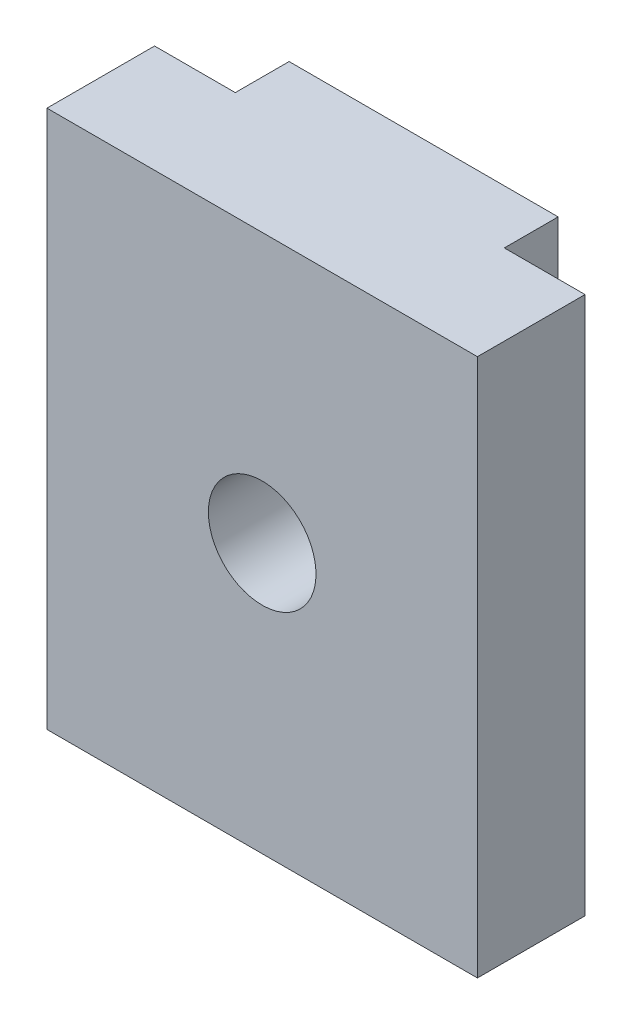
SolidWorks part; units mm, degrees
ref_plane "前视基准面" through (0, 0, 0) normal (0, 0, 1) x (1, 0, 0)
ref_plane "上视基准面" through (0, 0, 0) normal (0, 1, 0) x (1, 0, 0)
ref_plane "右视基准面" through (0, 0, 0) normal (1, 0, 0) x (0, 0, -1)
sketch "草图1" plane through (0, 0, 0) normal (0, 1, 0) x (1, 0, 0)
  line L0 (5, 2) -> (8, 2)
  line L1 (-8, 2) -> (-5, 2)
  line L2 (-8, 2) -> (-8, -2)
  line L3 (-8, -2) -> (8, -2)
  line L4 (8, 2) -> (8, -2)
  line L5 (-8, 2) -> (8, -2) construction
  line L6 (-8, -2) -> (8, 2) construction
  line L8 (5, 2) -> (5, 4)
  line L9 (5, 4) -> (-5, 4)
  line L10 (-5, 2) -> (-5, 4)
  point P0 (0, 0)
  dimension "D1" = 4
  dimension "D2" = 16
  dimension "D3" = 3
  dimension "D4" = 3
  dimension "D5" = 2
extrude "凸台-拉伸1" add sketch "草图1" along normal blind 20
sketch "草图4" plane through (0, 0, -4) normal (0, 0, -1) x (-1, 0, 0)
  line L0 (-5, 20) -> (5, 0)
  circle A0 centre (0, 10) radius 2
extrude "切除-拉伸2" cut sketch "草图4" against normal blind 20 contours L0 A0 | L0 A0
